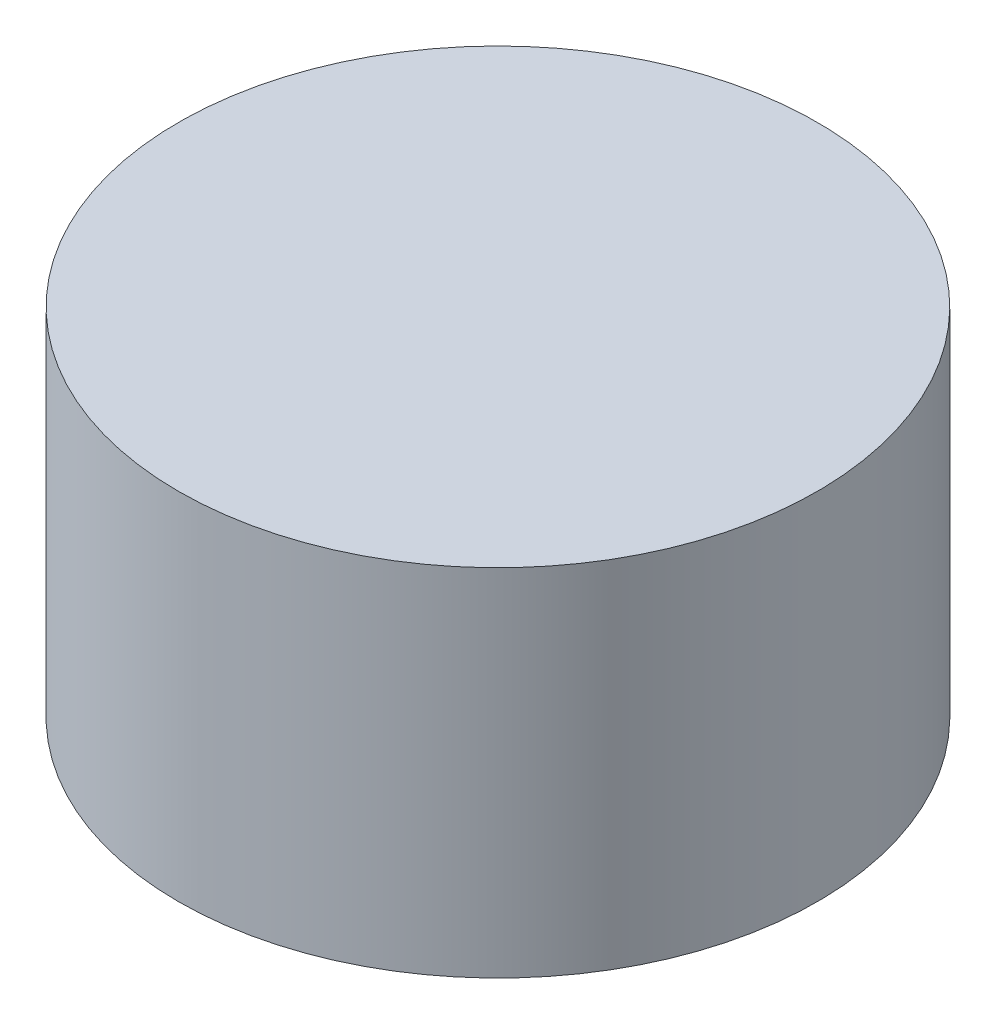
SolidWorks part; units mm, degrees
ref_plane "Front Plane" through (0, 0, 0) normal (0, 0, 1) x (1, 0, 0)
ref_plane "Top Plane" through (0, 0, 0) normal (0, 1, 0) x (1, 0, 0)
ref_plane "Right Plane" through (0, 0, 0) normal (1, 0, 0) x (0, 0, -1)
sketch "Sketch1" plane through (0, 0, 0) normal (0, 1, 0) x (1, 0, 0)
  circle A0 centre (0, 0) radius 35.9632
extrude "Boss-Extrude1" add sketch "Sketch1" along normal blind 40
